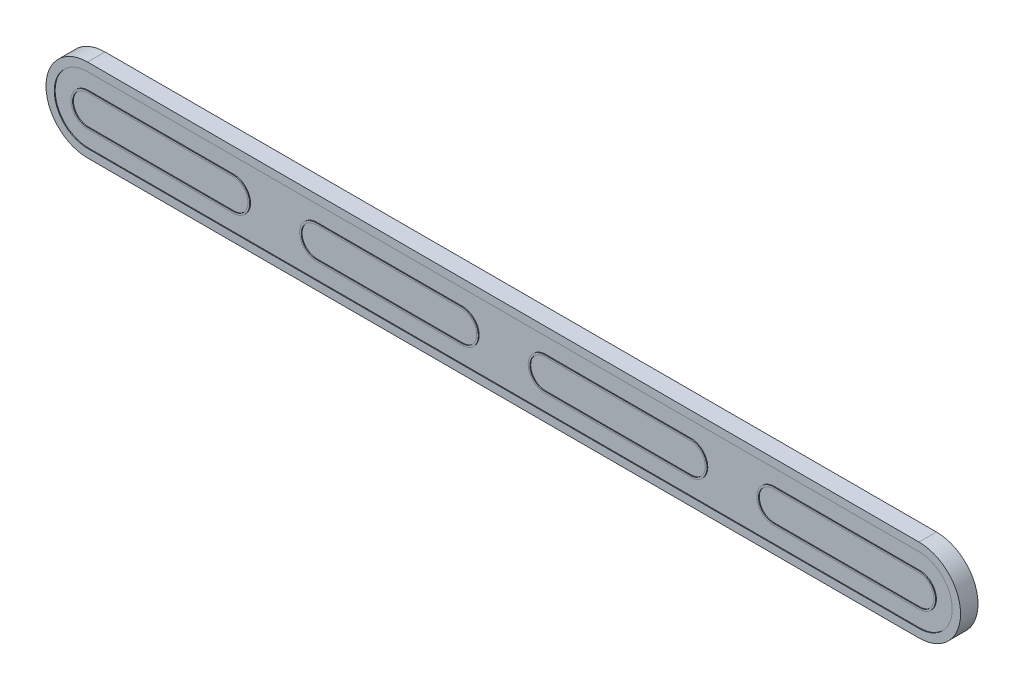
SolidWorks part; units mm, degrees
ref_plane "Front Plane" through (0, 0, 0) normal (0, 0, 1) x (1, 0, 0)
ref_plane "Top Plane" through (0, 0, 0) normal (0, 1, 0) x (1, 0, 0)
ref_plane "Right Plane" through (0, 0, 0) normal (1, 0, 0) x (0, 0, -1)
sketch "Sketch1" plane through (0, 0, 0) normal (0, 0, 1) x (1, 0, 0)
  line L0 (-50, 5) -> (50, 5)
  line L1 (-50, -5) -> (50, -5)
  arc A0 (-50, 5) -> (-50, -5) centre (-50, 0) ccw
  arc A1 (50, 5) -> (50, -5) centre (50, 0) cw
extrude "Extrude1" add sketch "Sketch1" along normal blind 2
sketch "Sketch2" plane through (0, 0, 2) normal (0, 0, 1) x (1, 0, 0)
  line L0 (-50, 5) -> (50, 5)
  line L1 (-50, -5) -> (50, -5)
  line L2 (-50, 4) -> (50, 4)
  line L3 (-50, -4) -> (50, -4)
  arc A0 (-50, 5) -> (-50, -5) centre (-50, 0) ccw
  arc A1 (50, 5) -> (50, -5) centre (50, 0) cw
  arc A2 (-50, 4) -> (-50, -4) centre (-50, 0) ccw
  arc A3 (50, 4) -> (50, -4) centre (50, 0) cw
  dimension "D2" = 1
  dimension "D1" = 1
extrude "Extrude2" add sketch "Sketch2" along normal blind 0.1
sketch "Sketch3" plane through (0, 0, 2) normal (0, 0, 1) x (1, 0, 0)
  line L0 (-50, 2) -> (-32.5, 2)
  line L1 (-50, -2) -> (-32.5, -2)
  line L2 (-22.5, 2) -> (-5, 2)
  line L3 (-22.5, -2) -> (-5, -2)
  line L4 (5, 2) -> (22.5, 2)
  line L5 (5, -2) -> (22.5, -2)
  line L6 (32.5, 2) -> (50, 2)
  line L7 (32.5, -2) -> (50, -2)
  line L9 (32.5, 1.8) -> (50, 1.8)
  line L10 (32.5, -1.8) -> (50, -1.8)
  line L11 (5, 1.8) -> (22.5, 1.8)
  line L12 (5, -1.8) -> (22.5, -1.8)
  line L13 (-50, 1.8) -> (-32.5, 1.8)
  line L14 (-50, -1.8) -> (-32.5, -1.8)
  line L15 (-22.5, 1.8) -> (-5, 1.8)
  line L16 (-22.5, -1.8) -> (-5, -1.8)
  arc A0 (-50, 2) -> (-50, -2) centre (-50, 0) ccw
  arc A1 (-32.5, 2) -> (-32.5, -2) centre (-32.5, 0) cw
  arc A2 (-22.5, 2) -> (-22.5, -2) centre (-22.5, 0) ccw
  arc A3 (-5, 2) -> (-5, -2) centre (-5, 0) cw
  arc A4 (5, 2) -> (5, -2) centre (5, 0) ccw
  arc A5 (22.5, 2) -> (22.5, -2) centre (22.5, 0) cw
  arc A6 (32.5, 2) -> (32.5, -2) centre (32.5, 0) ccw
  arc A7 (50, 2) -> (50, -2) centre (50, 0) cw
  arc A8 (32.5, -1.8) -> (32.5, 1.8) centre (32.5, 0) cw
  arc A9 (50, 1.8) -> (50, -1.8) centre (50, 0) cw
  arc A10 (22.5, 1.8) -> (22.5, -1.8) centre (22.5, 0) cw
  arc A11 (5, 1.8) -> (5, -1.8) centre (5, 0) ccw
  arc A12 (-5, 1.8) -> (-5, -1.8) centre (-5, 0) cw
  arc A13 (-22.5, 1.8) -> (-22.5, -1.8) centre (-22.5, 0) ccw
  arc A14 (-32.5, 1.8) -> (-32.5, -1.8) centre (-32.5, 0) cw
  arc A15 (-50, 1.8) -> (-50, -1.8) centre (-50, 0) ccw
  dimension "D3" = 10
  dimension "D6" = 1.8
  dimension "D1" = 2
  dimension "D2" = 2
  dimension "D4" = 10
  dimension "D5" = 10
extrude "Extrude3" add sketch "Sketch3" along normal blind 0.1
